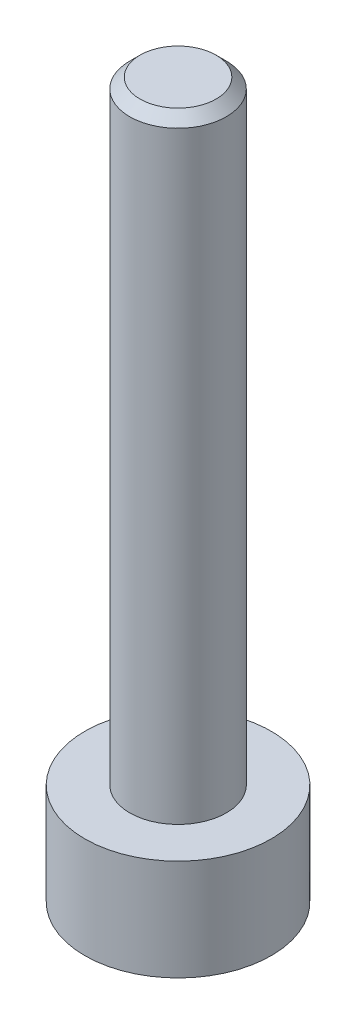
SolidWorks part; units mm, degrees
ref_plane "Front Plane" through (0, 0, 0) normal (0, 0, 1) x (1, 0, 0)
ref_plane "Top Plane" through (0, 0, 0) normal (0, 1, 0) x (1, 0, 0)
ref_plane "Right Plane" through (0, 0, 0) normal (1, 0, 0) x (0, 0, -1)
sketch "Sketch1" plane through (0, 0, 0) normal (0, 1, 0) x (1, 0, 0)
  circle A0 centre (0, 0) radius 1.825
  dimension "D1" = 3.65
extrude "Boss-Extrude1" add sketch "Sketch1" along normal blind 1.98
sketch "Sketch2" plane through (0, 1.98, 0) normal (0, 1, 0) x (1, 0, 0)
  circle A0 centre (0, 0) radius 0.945
  dimension "D1" = 1.89
extrude "Boss-Extrude2" add sketch "Sketch2" along normal blind 12
sketch "Sketch3" plane through (0, 0, 0) normal (0, -1, 0) x (1, 0, 0)
  line L1 (0.459, -0.795) -> (0.918, 0)
  line L2 (0.918, 0) -> (0.459, 0.795)
  line L3 (0.459, 0.795) -> (-0.459, 0.795)
  line L4 (-0.459, 0.795) -> (-0.918, 0)
  line L5 (-0.918, 0) -> (-0.459, -0.795)
  line L6 (-0.459, -0.795) -> (0.459, -0.795)
  circle A0 centre (0, 0) radius 0.795 construction
  dimension "D1" = 1.59
extrude "Cut-Extrude1" cut sketch "Sketch3" against normal blind 1
chamfer "Chamfer1" distance 0.2 angle 45 1 edges at (0, 13.98, 0.945)
